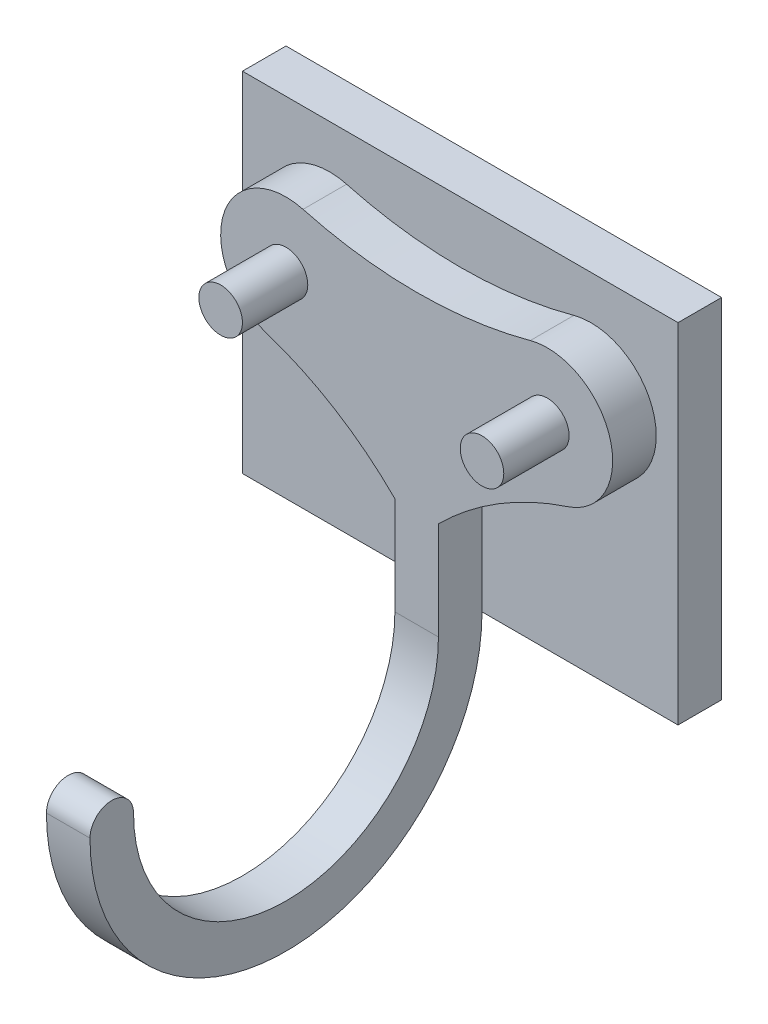
SolidWorks part; units mm, degrees
ref_plane "Alzado" through (0, 0, 0) normal (0, 0, 1) x (1, 0, 0)
ref_plane "Planta" through (0, 0, 0) normal (0, 1, 0) x (1, 0, 0)
ref_plane "Vista lateral" through (0, 0, 0) normal (1, 0, 0) x (0, 0, -1)
sketch "Croquis1" plane through (0, 0, 0) normal (0, 0, 1) x (1, 0, 0)
  line L1 (-10, 8) -> (10, 8)
  line L2 (-10, 8) -> (-10, -8)
  line L3 (-10, -8) -> (10, -8)
  line L4 (10, 8) -> (10, -8)
  point P0 (0, 0)
  dimension "D1" = 20
  dimension "D2" = 16
extrude "Saliente-Extruir1" add sketch "Croquis1" along normal blind 2 contours L1 L4 L3 L2
sketch "Croquis2" plane through (0, 0, 2) normal (0, 0, 1) x (1, 0, 0)
  line L0 (-10, 8) -> (10, 8) construction
  line L1 (-10, -8) -> (10, -8) construction
  line L3 (-1, -3.5) -> (-1, -8)
  line L4 (-1, -8) -> (1, -8)
  line L5 (1, -3.5) -> (1, -8)
  arc A0 (-5.2174, 5.8961) -> (-6.9349, 0.1494) centre (-6, 3) ccw
  arc A1 (6.9349, 0.1494) -> (5.2174, 5.8961) centre (6, 3) ccw
  arc A2 (-5.2174, 5.8961) -> (5.2174, 5.8961) centre (0, 25.2036) ccw
  arc A3 (6.9349, 0.1494) -> (1, -3.5) centre (11.6096, -14.1036) ccw
  arc A4 (-1, -3.5) -> (-6.9349, 0.1494) centre (-11.6096, -14.1036) ccw
  point P10 (0, -5.75)
  dimension "D1" = 6
  dimension "D2" = 6
  dimension "D7" = 20
  dimension "D10" = 15
  dimension "D11" = 4.5
  dimension "D12" = 15
  dimension "D3" = 6
  dimension "D4" = 6
  dimension "D5" = 5
  dimension "D6" = 5
  dimension "D8" = 2
  dimension "D9" = 0
extrude "Saliente-Extruir2" add sketch "Croquis2" along normal blind 2
sketch "Croquis3" plane through (0, 0, 4) normal (0, 0, 1) x (1, 0, 0)
  circle A0 centre (-6, 3) radius 1
  circle A1 centre (6, 3) radius 1
  arc A2 (-5.2174, 5.8961) -> (-6.9349, 0.1494) centre (-6, 3) ccw construction
  arc A3 (6.9349, 0.1494) -> (5.2174, 5.8961) centre (6, 3) ccw construction
  dimension "D1" = 2
  dimension "D2" = 2
extrude "Saliente-Extruir3" add sketch "Croquis3" along normal blind 3
sketch "Croquis5" plane through (-1, 0, 0) normal (-1, 0, 0) x (0, 0, 1)
  line L0 (4, -8) -> (2, -8) construction
  line L1 (2, 8) -> (2, -8) construction
  line L2 (-2.3309, -8) -> (22.8794, -8) construction
  line L3 (4, -8) -> (2, -8)
  arc A0 (2, -8) -> (20, -8) centre (11, -8) ccw
  arc A1 (4, -8) -> (18, -8) centre (11, -8) ccw
  arc A2 (20, -8) -> (18, -8) centre (19, -8) ccw
  dimension "D1" = 18
  dimension "D4" = 2
  dimension "D2" = 0
extrude "Saliente-Extruir4" add sketch "Croquis5" against normal blind 2
